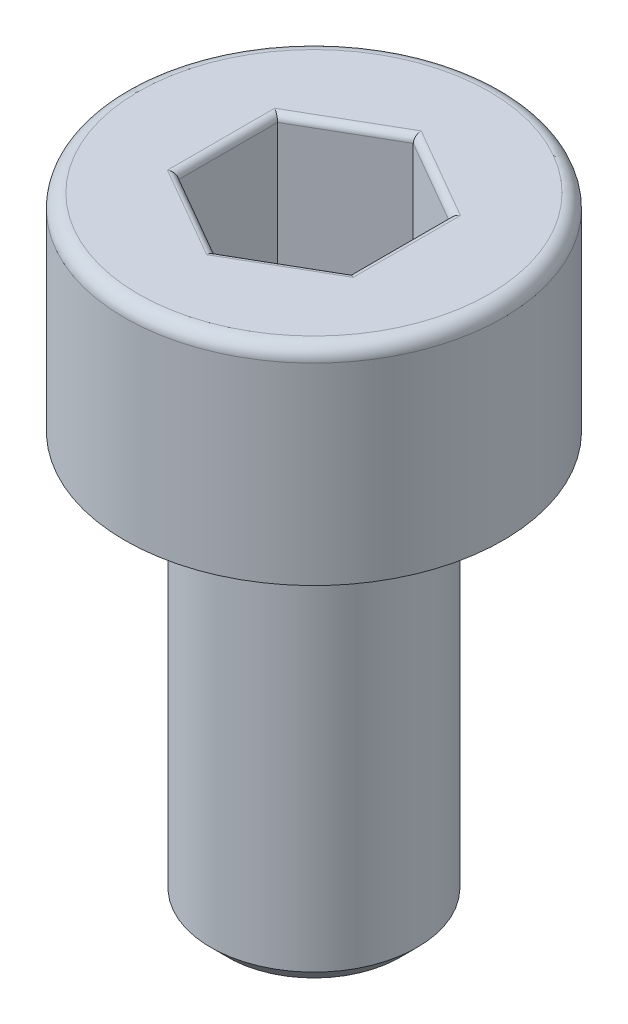
SolidWorks part; units mm, degrees
ref_plane "Front Plane" through (0, 0, 0) normal (0, 0, 1) x (1, 0, 0)
ref_plane "Top Plane" through (0, 0, 0) normal (0, 1, 0) x (1, 0, 0)
ref_plane "Right Plane" through (0, 0, 0) normal (1, 0, 0) x (0, 0, -1)
sketch "Sketch1" plane through (0, 0, 0) normal (0, 0, 1) x (1, 0, 0)
  line L0 (0, 0) -> (0, -47.0967) construction
  line L1 (0, -9) -> (-1.5, -9)
  line L2 (-1.5, -9) -> (-1.5, -3)
  line L3 (-1.5, -3) -> (-2.75, -3)
  line L4 (-2.75, -3) -> (-2.75, 0)
  line L5 (-2.75, 0) -> (0, 0)
  line L6 (0, 0) -> (0, -9)
  dimension "D1" = 6
  dimension "d" = 3
  dimension "k" = 3
  dimension "dk" = 5.5
revolve "Revolve1" add sketch "Sketch1" angle 360 about L0
chamfer "Chamfer1" distance 0.25 angle 45 2 edges at (0, -3, 1.5) (0, -9, 1.5)
fillet "Fillet1" radius 0.2 1 edges at (0, 0, 2.75)
sketch "Sketch2" plane through (0, 0, 0) normal (0, 1, 0) x (1, 0, 0)
  line L1 (0, 1.4434) -> (-1.25, 0.7217)
  line L2 (-1.25, 0.7217) -> (-1.25, -0.7217)
  line L3 (-1.25, -0.7217) -> (0, -1.4434)
  line L4 (0, -1.4434) -> (1.25, -0.7217)
  line L5 (1.25, -0.7217) -> (1.25, 0.7217)
  line L6 (1.25, 0.7217) -> (0, 1.4434)
  circle A0 centre (0, 0) radius 1.25 construction
  dimension "s" = 2.5
extrude "Cut-Extrude1" cut sketch "Sketch2" against normal blind 2
fillet "Fillet2" radius 0.1 12 edges at (-0.625, 0, -1.0825) (-1.25, 0, 0) (-0.625, 0, 1.0825) (0.625, 0, 1.0825) (1.25, 0, 0) (0.625, 0, -1.0825) (1.25, -2, 0) (0.625, -2, 1.0825) (-0.625, -2, 1.0825) (-1.25, -2, 0) (-0.625, -2, -1.0825) (0.625, -2, -1.0825)
